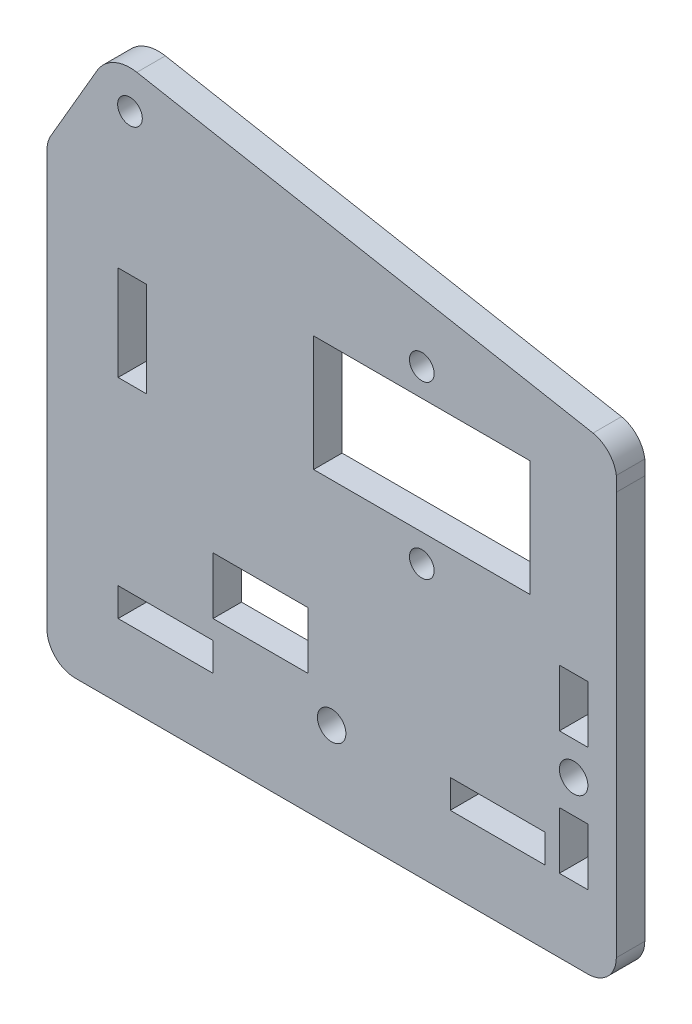
SolidWorks part; units mm, degrees
ref_plane "Front Plane" through (0, 0, 0) normal (0, 0, 1) x (1, 0, 0)
ref_plane "Top Plane" through (0, 0, 0) normal (0, 1, 0) x (1, 0, 0)
ref_plane "Right Plane" through (0, 0, 0) normal (1, 0, 0) x (0, 0, -1)
sketch "Model" plane through (0, 0, 0) normal (0, 0, 1) x (1, 0, 0)
  line L0 (21.9627, 39.5808) -> (21.9628, 58.4959)
  line L1 (21.9627, 14.7959) -> (21.9627, 39.5808)
  line L2 (78.9625, 11.7959) -> (24.9625, 11.7959)
  line L3 (25.4277, 65.2695) -> (22.3687, 60.0027)
  line L5 (29.4626, 51.4959) -> (32.4626, 51.4959)
  line L6 (29.4626, 51.4959) -> (29.4626, 41.4959)
  line L7 (29.4626, 41.4959) -> (32.4626, 41.4959)
  line L8 (32.4626, 51.4959) -> (32.4626, 41.4959)
  line L12 (39.4626, 19.4959) -> (39.4626, 22.4959)
  line L13 (29.4626, 19.4959) -> (39.4626, 19.4959)
  line L14 (29.4626, 22.4959) -> (29.4626, 19.4959)
  line L15 (39.4626, 22.4959) -> (29.4626, 22.4959)
  line L16 (64.4626, 19.4959) -> (74.4626, 19.4959)
  line L17 (64.4626, 22.4959) -> (64.4626, 19.4959)
  line L18 (74.4626, 22.4959) -> (64.4626, 22.4959)
  line L19 (74.4626, 19.4959) -> (74.4626, 22.4959)
  line L20 (75.9626, 25.4956) -> (78.9626, 25.4956)
  line L21 (75.9626, 19.4956) -> (75.9626, 25.4956)
  line L22 (78.9626, 19.4956) -> (75.9626, 19.4956)
  line L23 (78.9626, 25.4956) -> (78.9626, 19.4956)
  line L24 (72.8627, 55.5958) -> (50.0627, 55.5958)
  line L25 (72.8627, 43.3958) -> (72.8627, 55.5958)
  line L26 (50.0627, 43.3958) -> (72.8627, 43.3958)
  line L27 (50.0627, 55.5958) -> (50.0627, 43.3958)
  line L28 (75.9626, 32.4956) -> (75.9626, 38.4956)
  line L29 (78.9626, 32.4956) -> (75.9626, 32.4956)
  line L30 (78.9626, 38.4956) -> (78.9626, 32.4956)
  line L31 (75.9626, 38.4956) -> (78.9626, 38.4956)
  line L32 (27.2516, 68.4097) -> (25.4277, 65.2695)
  line L33 (79.5083, 61.4456) -> (31.4378, 70.334)
  line L34 (81.9893, 57.2955) -> (81.9635, 58.8096)
  line L35 (81.9628, 14.7957) -> (81.9893, 57.2955)
  line L36 (50.0627, 49.4958) -> (72.8627, 49.4958) construction
  line L37 (61.4627, 55.5958) -> (61.4627, 43.3958) construction
  line L39 (39.4627, 30.4959) -> (49.4627, 30.4959)
  line L40 (39.4627, 30.4959) -> (39.4627, 24.4959)
  line L41 (39.4627, 24.4959) -> (49.4627, 24.4959)
  line L42 (49.4627, 30.4959) -> (49.4627, 24.4959)
  circle A0 centre (61.4627, 58.4958) radius 1.3
  circle A1 centre (61.4627, 40.4958) radius 1.3
  circle A2 centre (30.7105, 66.4007) radius 1.3
  circle A3 centre (51.9627, 20.9958) radius 1.5
  circle A4 centre (77.4626, 28.9956) radius 1.5
  arc A6 (22.3687, 60.0027) -> (21.9628, 58.4959) centre (24.9632, 58.4957) ccw
  arc A7 (21.9627, 14.7959) -> (24.9625, 11.7959) centre (24.9626, 14.7959) ccw
  arc A8 (31.4378, 70.334) -> (27.2516, 68.4097) centre (30.7105, 66.4006) ccw
  arc A9 (81.9635, 58.8096) -> (79.5083, 61.4456) centre (78.8528, 58.3737) ccw
  arc A10 (78.9625, 11.7959) -> (81.9628, 14.7957) centre (78.9625, 14.7961) ccw
  dimension "D5" = 3
  dimension "D6" = 2.6
  dimension "D7" = 3
  dimension "D8" = 3
  dimension "D9" = 18
  dimension "D10" = 10
  dimension "D19" = 10
  dimension "D3" = 10
  dimension "D4" = 3
  dimension "D11" = 12.2
  dimension "D12" = 22.8
  dimension "D13" = 6
  dimension "D14" = 3
  dimension "D15" = 3
  dimension "D16" = 10
  dimension "D17" = 3
  dimension "D18" = 6
  dimension "D20" = 6
  dimension "D21" = 2
  dimension "D22" = 19
  dimension "D23" = 7.6997
extrude "Boss-Extrude1" add sketch "Model" along normal blind 3
